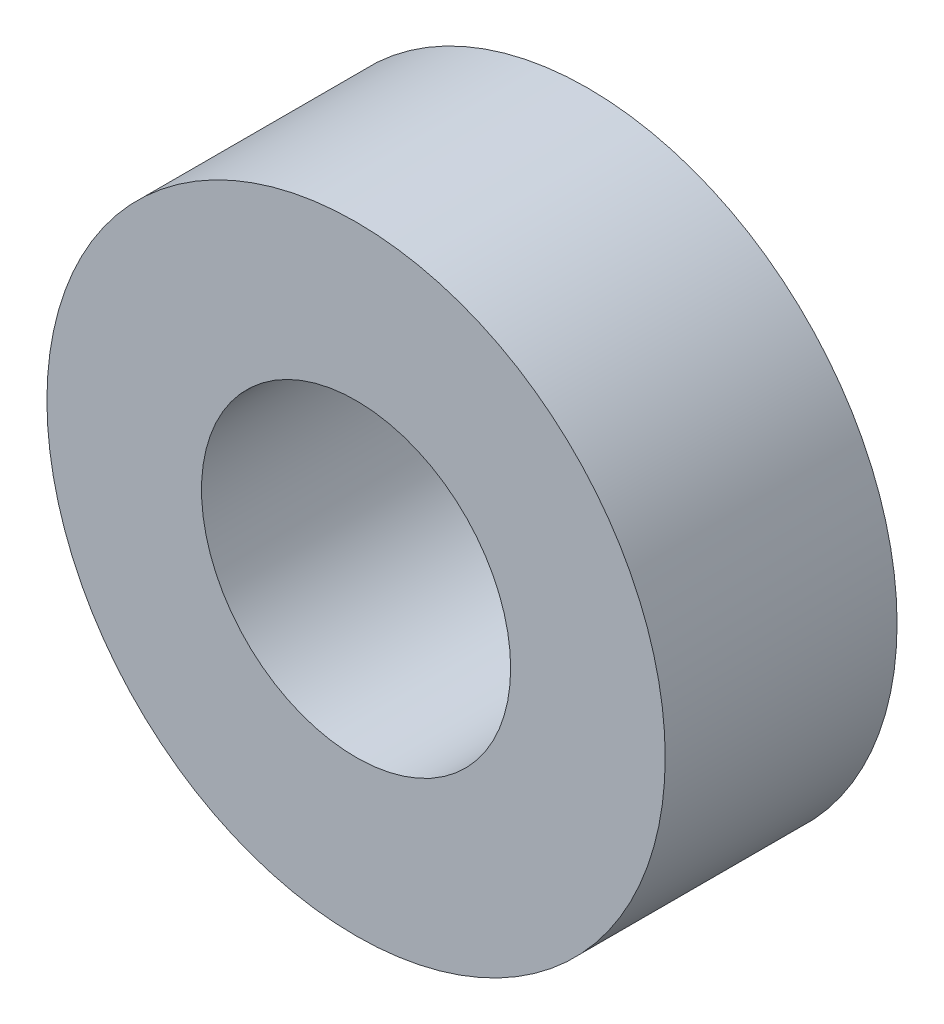
SolidWorks part; units mm, degrees
material "POLYURETHANE (11671)"
ref_plane "Front Plane" through (0, 0, 0) normal (0, 0, 1) x (1, 0, 0)
ref_plane "Top Plane" through (0, 0, 0) normal (0, 1, 0) x (1, 0, 0)
ref_plane "Right Plane" through (0, 0, 0) normal (1, 0, 0) x (0, 0, -1)
sketch "Sketch2" plane through (0, 0, 4.7625) normal (0, 0, 1) x (1, 0, 0)
  circle A0 centre (290.3087, 659.2798) radius 3.175 construction
  circle A1 centre (290.3087, 659.2798) radius 3.175
  circle A2 centre (290.3087, 659.2798) radius 6.35
  dimension "D1" = 12.7
extrude "Boss-Extrude1" add sketch "Sketch2" along normal blind 4.7625
